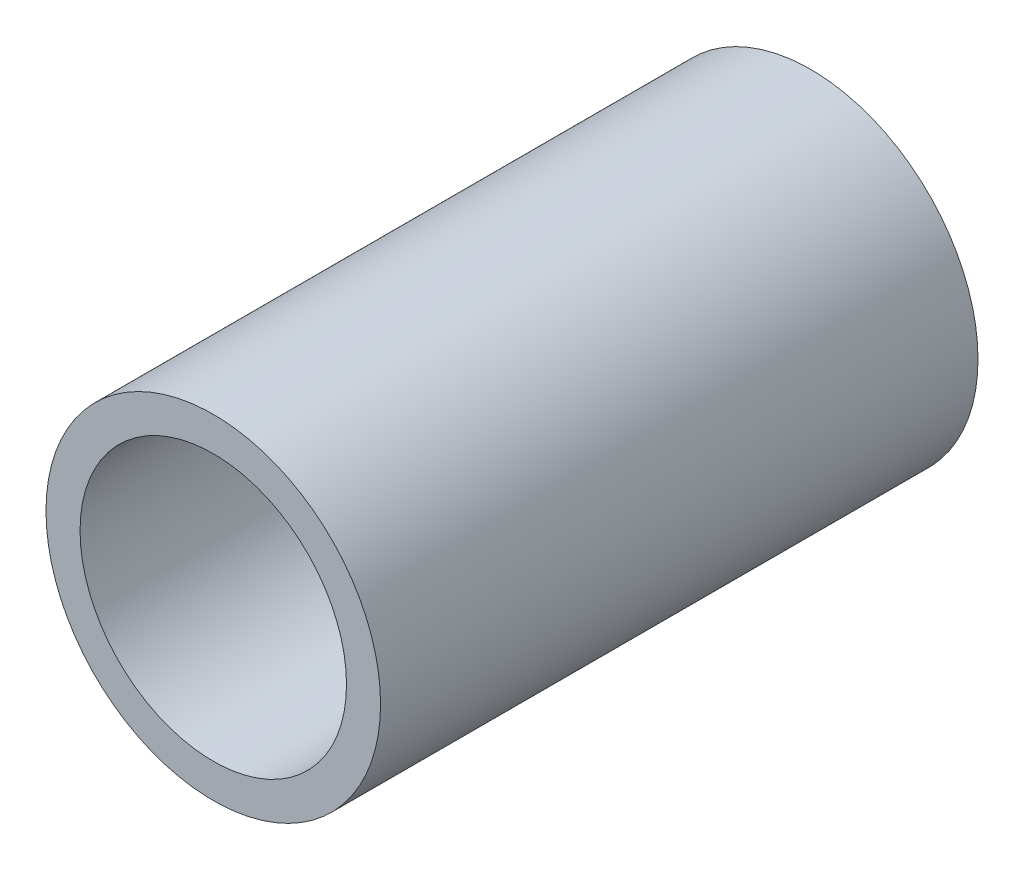
SolidWorks part; units mm, degrees
ref_plane "Plano frontal" through (0, 0, 0) normal (0, 0, 1) x (1, 0, 0)
ref_plane "Plano superior" through (0, 0, 0) normal (0, 1, 0) x (1, 0, 0)
ref_plane "Plano direito" through (0, 0, 0) normal (1, 0, 0) x (0, 0, -1)
sketch "Esboço1" plane through (0, 0, 0) normal (0, 0, 1) x (1, 0, 0)
  circle A0 centre (2.2536, 0) radius 11.15
  circle A1 centre (2.2536, 0) radius 14
extrude "Ressalto-extrusão1" add sketch "Esboço1" along normal blind 50
